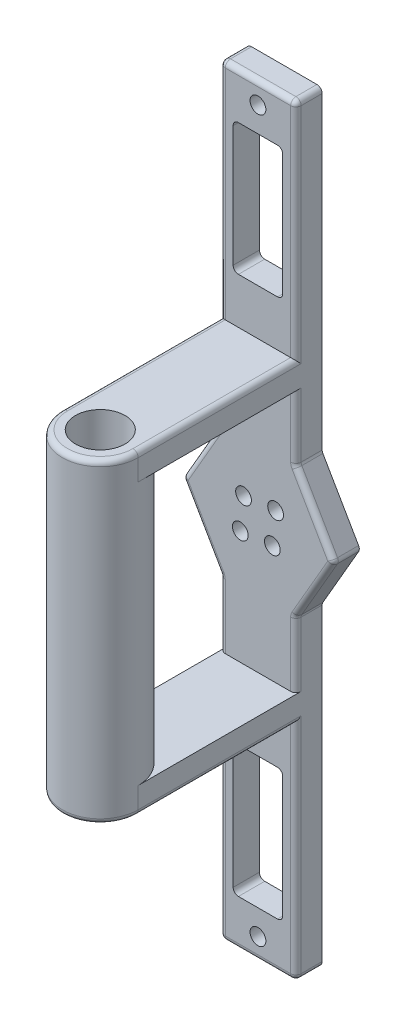
SolidWorks part; units mm, degrees
ref_plane "Спереди" through (0, 0, 0) normal (0, 0, 1) x (1, 0, 0)
ref_plane "Сверху" through (0, 0, 0) normal (0, 1, 0) x (1, 0, 0)
ref_plane "Справа" through (0, 0, 0) normal (1, 0, 0) x (0, 0, -1)
other "Configuration Table"
sketch "Sketch1" plane through (0, 0, 0) normal (0, 0, 1) x (1, 0, 0)
  line L1 (14.4338, 25) -> (-14.4338, 25)
  line L2 (-14.4338, 25) -> (-28.8675, 0)
  line L3 (-28.8675, 0) -> (-14.4338, -25)
  line L4 (-14.4338, -25) -> (14.4338, -25)
  line L5 (14.4338, -25) -> (28.8675, 0)
  line L6 (28.8675, 0) -> (14.4338, 25)
  circle A1 centre (0, 0) radius 25 construction
  dimension "D1" = 50
extrude "Boss-Extrude2" add sketch "Sketch1" along normal blind 10
sketch "Sketch2" plane through (0, 0, 10) normal (0, 0, 1) x (1, 0, 0)
  line L0 (0, 0) -> (-30.4359, 0) construction
  line L1 (0, 0) -> (-15.0629, 15.0629) construction
  line L2 (0, 0) -> (12.64, 12.64) construction
  circle A0 centre (-5.4801, 5.4801) radius 3
  circle A1 centre (6.7175, 6.7175) radius 3
  circle A2 centre (5.4801, -5.4801) radius 3
  circle A3 centre (-6.7175, -6.7175) radius 3
  point P13 (0, 0)
  point P14 (0, 0)
  dimension "D2" = 6
  dimension "D1" = 45
  dimension "D3" = 19
  dimension "D4" = 15.5
extrude "Cut-Extrude1" cut sketch "Sketch2" against normal blind 5
sketch "Sketch3" plane through (0, 0, 5) normal (0, 0, 1) x (1, 0, 0)
  circle A0 centre (-5.4801, 5.4801) radius 1.5
  circle A1 centre (6.7175, 6.7175) radius 1.5
  circle A2 centre (5.4801, -5.4801) radius 1.5
  circle A3 centre (-6.7175, -6.7175) radius 1.5
  dimension "D1" = 3
extrude "Cut-Extrude2" cut sketch "Sketch3" against normal up to next
sketch "Sketch4" plane through (0, 0, 0) normal (0, 0, -1) x (-1, 0, 0)
  line L0 (0, 0) -> (0, 40.6349) construction
  line L1 (-56.6567, 0) -> (54.1025, 0) construction
  line L2 (-14.4338, 25) -> (14.4338, 25) construction
  line L3 (-14.4338, 25) -> (14.4338, 25)
  line L4 (-14.4338, 25) -> (-14.4338, 145)
  line L5 (-14.4338, 145) -> (14.4338, 145)
  line L6 (14.4338, 25) -> (14.4338, 145)
  line L7 (-14.4338, -145) -> (14.4338, -145)
  line L8 (14.4338, -25) -> (14.4338, -145)
  line L9 (-14.4338, -25) -> (14.4338, -25)
  line L10 (-14.4338, -25) -> (-14.4338, -145)
  line L11 (0, 145) -> (0, 121.9848) construction
  circle A0 centre (0, 137) radius 1.5
  circle A1 centre (0, -137) radius 1.5
  point P19 (0, 0)
  point P20 (0, 136.2796)
  point P23 (-10.8861, 25)
  dimension "D3" = 3
  dimension "D2" = 120
  dimension "D4" = 137
extrude "Boss-Extrude4" add sketch "Sketch4" against normal up to surface (10 mm away) up to face at (-3.7175, -6.7175, 10)
sketch "Sketch5" plane through (0, 0, 10) normal (0, 0, 1) x (1, 0, 0)
  circle A0 centre (0, 137) radius 3
  circle A1 centre (0, -137) radius 3
  dimension "D1" = 6
  dimension "D2" = 6
extrude "Cut-Extrude3" cut sketch "Sketch5" against normal blind 5
sketch "Sketch6" plane through (0, 0, 0) normal (0, 0, -1) x (-1, 0, 0)
  line L0 (-44.6052, 0) -> (88.3819, 0) construction
  line L1 (0, 145) -> (0, 120.7707) construction
  line L2 (14.4338, 145) -> (-14.4338, 145) construction
  line L3 (0, 137) -> (-4.1294, 137) construction
  line L4 (3, 138) -> (7, 138)
  line L5 (-1, 140) -> (1, 140)
  line L6 (-1, 140) -> (-1, 144)
  line L7 (-1, 144) -> (1, 144)
  line L8 (1, 140) -> (1, 144)
  line L9 (-1, 140) -> (1, 144) construction
  line L10 (-1, 144) -> (1, 140) construction
  line L11 (3, 138) -> (3, 136)
  line L12 (3, 136) -> (7, 136)
  line L13 (7, 138) -> (7, 136)
  line L14 (1, 134) -> (1, 130)
  line L15 (1, 134) -> (-1, 134)
  line L16 (-1, 134) -> (-1, 130)
  line L17 (1, 130) -> (-1, 130)
  line L18 (-3, 136) -> (-7, 136)
  line L19 (-3, 136) -> (-3, 138)
  line L20 (-3, 138) -> (-7, 138)
  line L21 (-7, 136) -> (-7, 138)
  line L22 (1, -134) -> (-1, -134)
  line L23 (-1, -134) -> (-1, -130)
  line L24 (1, -130) -> (-1, -130)
  line L25 (1, -134) -> (1, -130)
  line L26 (3, -138) -> (3, -136)
  line L27 (3, -136) -> (7, -136)
  line L28 (7, -138) -> (7, -136)
  line L29 (3, -138) -> (7, -138)
  line L30 (-3, -136) -> (-3, -138)
  line L31 (-3, -138) -> (-7, -138)
  line L32 (-7, -136) -> (-7, -138)
  line L33 (-3, -136) -> (-7, -136)
  line L34 (-1, -144) -> (1, -144)
  line L35 (1, -140) -> (1, -144)
  line L36 (-1, -140) -> (1, -140)
  line L37 (-1, -140) -> (-1, -144)
  point P10 (0, 142)
  point P15 (0, 137)
  point P31 (0, 137)
  dimension "D1" = 4
  dimension "D2" = 2
  dimension "D3" = 3
  dimension "D4" = 4
extrude "Cut-Extrude4" cut sketch "Sketch6" against normal blind 4
sketch "Sketch7" plane through (0, 0, 0) normal (0, 1, 0) x (1, 0, 0)
  line L0 (-14.4338, -10) -> (14.4338, -10) construction
  line L1 (0, 0) -> (0, -70) construction
  line L2 (14.4338, -10) -> (14.4338, -85.4462) construction
  circle A0 centre (0, -70) radius 14.4338
  dimension "D2" = 60
extrude "Boss-Extrude5" add sketch "Sketch7" along normal mid plane 120 separate body
sketch "Sketch8" plane through (0, -60, 0) normal (0, -1, 0) x (1, 0, 0)
  circle A0 centre (0, 70) radius 9.4338
  circle A1 centre (0, 70) radius 14.4338 construction
  dimension "D1" = 5
extrude "Cut-Extrude6" cut sketch "Sketch8" against normal up to next (120 mm away)
sketch "Sketch11" plane through (0, 0, 10) normal (0, 0, 1) x (1, 0, 0)
  line L1 (14.4338, 50) -> (-14.4338, 50)
  line L2 (14.4338, 50) -> (14.4338, 60)
  line L3 (14.4338, 60) -> (-14.4338, 60)
  line L4 (-14.4338, 50) -> (-14.4338, 60)
  line L5 (14.4338, 50) -> (-14.4338, 60) construction
  line L6 (14.4338, 60) -> (-14.4338, 50) construction
  line L7 (0, 60) -> (0, 67.4424) construction
  line L8 (14.4338, 60) -> (-14.4338, 60) construction
  point P0 (0, 55)
  point P5 (0, 67.4424)
  point P7 (0, 60)
  point P11 (12.2386, 60)
  dimension "D1" = 10
extrude "Boss-Extrude6" add sketch "Sketch11" along normal up to surface (60 mm away)
mirror "Mirror1" about plane through (0, 0, 0) normal (0, 1, 0) of "Boss-Extrude6"
sketch "Sketch13" plane through (0, 0, 10) normal (0, 0, 1) x (1, 0, 0)
  line L0 (14.4338, 145) -> (14.4338, 60) construction
  line L1 (9.4338, 77.5) -> (-9.4338, 77.5)
  line L2 (9.4338, 77.5) -> (9.4338, 127.5)
  line L3 (9.4338, 127.5) -> (-9.4338, 127.5)
  line L4 (-9.4338, 77.5) -> (-9.4338, 127.5)
  line L5 (9.4338, 77.5) -> (-9.4338, 127.5) construction
  line L6 (9.4338, 127.5) -> (-9.4338, 77.5) construction
  line L7 (0, 145) -> (0, 62.8418) construction
  line L8 (-14.4338, 145) -> (14.4338, 145) construction
  line L9 (-14.4338, 102.5) -> (14.4338, 102.5) construction
  line L10 (-14.4338, 60) -> (-14.4338, 145) construction
  line L11 (-28.8675, 0) -> (62.8003, 0) construction
  line L12 (9.4338, -127.5) -> (-9.4338, -127.5)
  line L13 (-9.4338, -77.5) -> (-9.4338, -127.5)
  line L14 (9.4338, -77.5) -> (-9.4338, -77.5)
  line L15 (9.4338, -77.5) -> (9.4338, -127.5)
  point P0 (0, 102.5)
  dimension "D1" = 5
  dimension "D2" = 50
extrude "Cut-Extrude7" cut sketch "Sketch13" against normal up to next
fillet "Fillet3" radius 2 24 edges at (28.8675, 0, 5) (14.4338, -25, 5) (-14.4338, -25, 5) (-28.8675, 0, 5) (-14.4338, 25, 5) (14.4338, 25, 5) (14.4338, 60, 40) (-14.4338, 60, 40) (0, 60, 84.4338) (0, -60, 84.4338) (-14.4338, -60, 40) (14.4338, -60, 40) (-9.4338, 77.5, 5) (-9.4338, 127.5, 5) (9.4338, 127.5, 5) (9.4338, 77.5, 5) (9.4338, -77.5, 5) (9.4338, -127.5, 5) (-9.4338, -127.5, 5) (-9.4338, -77.5, 5) (14.4338, 145, 5) (-14.4338, 145, 5) (14.4338, -145, 5) (-14.4338, -145, 5)
fillet "Fillet4" radius 2 28 edges at (14.4338, 37.7679, 10) (-14.4338, 100.5, 10) (-14.4338, -37.7679, 10) (14.4338, -100.5, 10) (-14.4338, 37.7679, 10) (14.4338, 100.5, 10) (21.4959, 12.7679, 10) (0, 145, 10) (13.848, 144.4142, 10) (-13.848, 144.4142, 10) (-21.4959, 12.7679, 10) (-21.4959, -12.7679, 10) (14.4338, -37.7679, 10) (21.4959, -12.7679, 10) (28.5581, 0, 10) (-28.5581, 0, 10) (-14.4338, -100.5, 10) (0, -145, 10) (13.848, -144.4142, 10) (-13.848, -144.4142, 10) (-13.848, 59.4142, 10) (13.848, 59.4142, 10) (14.5019, 25.0183, 10) (-14.5019, 25.0183, 10) (-14.5019, -25.0183, 10) (14.5019, -25.0183, 10) (13.848, -59.4142, 10) (-13.848, -59.4142, 10)
